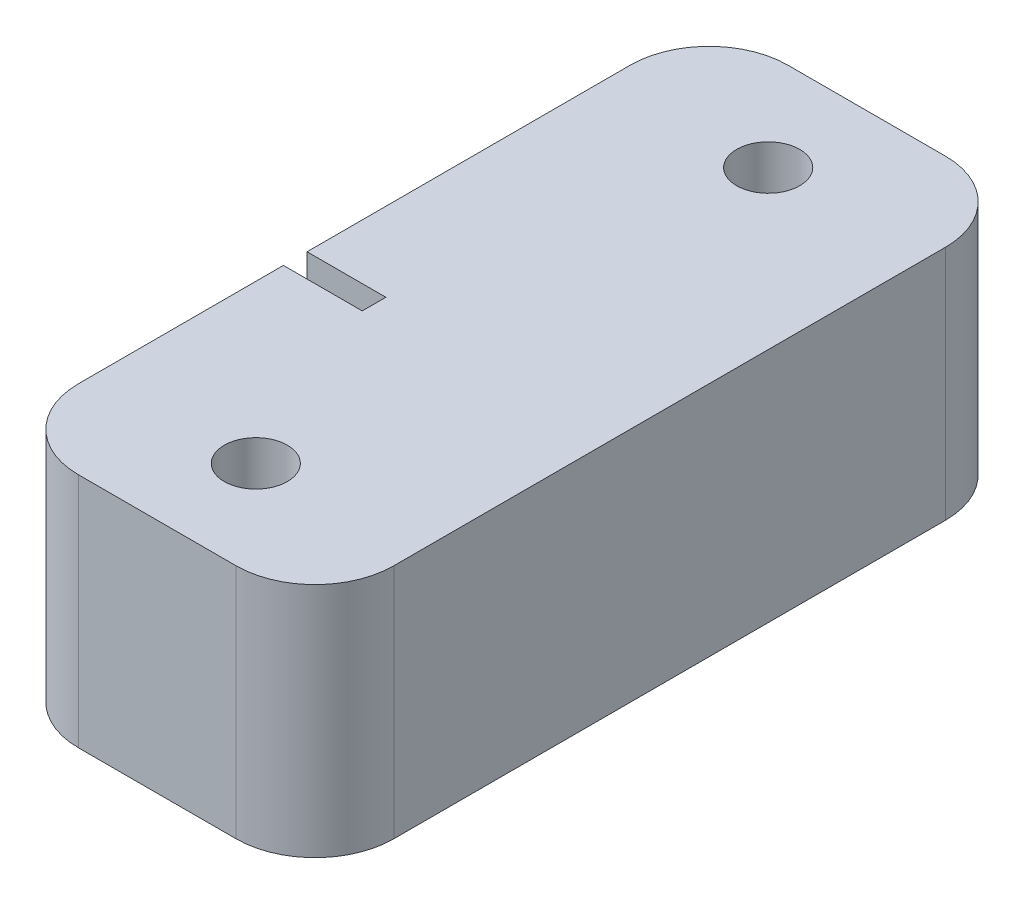
SolidWorks part; units mm, degrees
ref_plane "Front Plane" through (0, 0, 0) normal (0, 0, 1) x (1, 0, 0)
ref_plane "Top Plane" through (0, 0, 0) normal (0, 1, 0) x (1, 0, 0)
ref_plane "Right Plane" through (0, 0, 0) normal (1, 0, 0) x (0, 0, -1)
sketch "Sketch2" plane through (0, 0, 0) normal (0, 1, 0) x (1, 0, 0)
  line L1 (-23.5224, 49.7612) -> (16.4776, 49.7612)
  line L2 (-23.5224, 49.7612) -> (-23.5224, -40.2388)
  line L3 (-23.5224, -40.2388) -> (16.4776, -40.2388)
  line L4 (16.4776, 49.7612) -> (16.4776, -40.2388)
  dimension "D1" = 90
  dimension "D2" = 40
extrude "Boss-Extrude1" add sketch "Sketch2" along normal blind 30
sketch "Sketch3" plane through (0, 30, 0) normal (0, 1, 0) x (1, 0, 0)
  line L3 (16.4776, -40.2388) -> (16.4776, 49.7612) construction
  line L5 (16.4776, 49.7612) -> (-23.5224, 49.7612) construction
  circle A0 centre (-3.5224, 37.2612) radius 4
  circle A1 centre (-3.5224, -27.7388) radius 4
  dimension "D13" = 8
  dimension "D14" = 8
  dimension "D2" = 65
  dimension "D3" = 12.5
  dimension "D5" = 20
extrude "Cut-Extrude1" cut sketch "Sketch3" against normal blind 20
sketch "Sketch4" plane through (-23.5224, 0, 0) normal (-1, 0, 0) x (0, 0, 1)
  line L0 (40.2388, 30) -> (40.2388, 0) construction
  line L5 (-49.7612, 30) -> (40.2388, 30) construction
  line L7 (1.2388, 30) -> (4.2388, 30)
  line L8 (1.2388, 30) -> (1.2388, 18)
  line L9 (1.2388, 18) -> (4.2388, 18)
  line L10 (4.2388, 30) -> (4.2388, 18)
  circle A2 centre (2.7388, 15) radius 2.5
  circle A3 centre (2.7388, 15) radius 4
  point P4 (2.7388, 18)
  dimension "D2" = 8
  dimension "D3" = 37.5
  dimension "D1" = 5
  dimension "D4" = 15
  dimension "D5" = 12
  dimension "D6" = 0
  dimension "D7" = 3
extrude "Cut-Extrude2" cut sketch "Sketch4" against normal blind 10
fillet "Fillet1" radius 10 4 edges at (-23.5224, 15, -49.7612) (16.4776, 15, -49.7612) (16.4776, 15, 40.2388) (-23.5224, 15, 40.2388)
